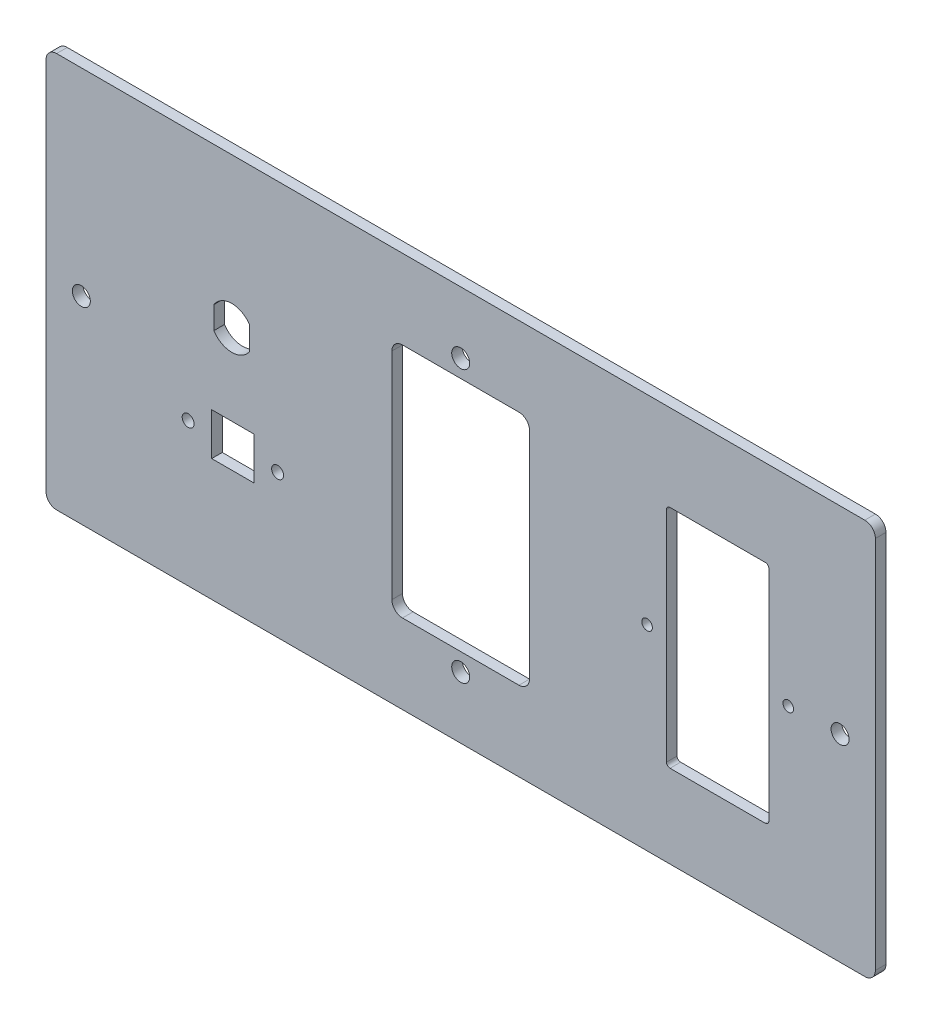
SolidWorks part; units mm, degrees
ref_plane "Front Plane" through (0, 0, 0) normal (0, 0, 1) x (1, 0, 0)
ref_plane "Top Plane" through (0, 0, 0) normal (0, 1, 0) x (1, 0, 0)
ref_plane "Right Plane" through (0, 0, 0) normal (1, 0, 0) x (0, 0, -1)
sketch "Sketch1" plane through (0, 0, 0) normal (0, 0, 1) x (1, 0, 0)
  line L0 (405.8623, -19.6394) -> (405.8623, -13.2354)
  line L1 (482.1408, 3.5626) -> (449.1408, 3.5626)
  line L2 (485.1408, 0.5626) -> (485.1408, -60.4374)
  line L3 (482.1408, -63.4374) -> (449.1408, -63.4374)
  line L4 (401.0848, -35.0851) -> (401.0848, -64.7571) construction
  line L5 (395.0848, -39.3556) -> (407.0848, -39.3556)
  line L6 (395.0848, -39.3556) -> (395.0848, -51.3556)
  line L7 (446.1408, 0.5626) -> (446.1408, -60.4374)
  line L8 (485.1408, 3.5626) -> (446.1408, -63.4374) construction
  line L9 (485.1408, -63.4374) -> (446.1408, 3.5626) construction
  line L11 (395.714, -13.2354) -> (395.714, -19.6394)
  line L19 (395.0848, -51.3556) -> (407.0848, -51.3556)
  line L21 (407.0848, -39.3556) -> (407.0848, -51.3556)
  line L22 (421.0756, -45.3556) -> (378.9661, -45.3556) construction
  line L24 (551.9531, 1.5878) -> (524.9531, 1.5878)
  line L25 (552.9531, 0.5878) -> (552.9531, -61.4122)
  line L26 (551.9531, -62.4122) -> (524.9531, -62.4122)
  line L27 (523.9531, 0.5878) -> (523.9531, -61.4122)
  line L28 (552.9531, 1.5878) -> (523.9531, -62.4122) construction
  line L29 (552.9531, -62.4122) -> (523.9531, 1.5878) construction
  line L30 (580.1408, 26.0626) -> (351.1408, 26.0626)
  line L31 (583.1408, 23.0626) -> (583.1408, -82.9374)
  line L32 (580.1408, -85.9374) -> (351.1408, -85.9374)
  line L33 (348.1408, 23.0626) -> (348.1408, -82.9374)
  line L34 (583.1408, 26.0626) -> (348.1408, -85.9374) construction
  line L35 (583.1408, -85.9374) -> (348.1408, 26.0626) construction
  arc A0 (446.1408, 0.5626) -> (449.1408, 3.5626) centre (449.1408, 0.5626) cw
  arc A1 (449.1408, -63.4374) -> (446.1408, -60.4374) centre (449.1408, -60.4374) cw
  arc A2 (482.1408, -63.4374) -> (485.1408, -60.4374) centre (482.1408, -60.4374) ccw
  arc A3 (485.1408, 0.5626) -> (482.1408, 3.5626) centre (482.1408, 0.5626) ccw
  circle A4 centre (465.6408, 8.5626) radius 2.55
  circle A5 centre (465.6408, -68.4374) radius 2.55
  arc A6 (405.8623, -13.2354) -> (395.714, -13.2354) centre (400.7881, -16.4374) ccw
  arc A7 (395.714, -19.6394) -> (405.8623, -19.6394) centre (400.7881, -16.4374) ccw
  circle A16 centre (388.4102, -45.3556) radius 1.69
  circle A17 centre (413.7594, -45.3556) radius 1.69
  arc A18 (552.9531, -61.4122) -> (551.9531, -62.4122) centre (551.9531, -61.4122) cw
  arc A19 (524.9531, -62.4122) -> (523.9531, -61.4122) centre (524.9531, -61.4122) cw
  arc A20 (523.9531, 0.5878) -> (524.9531, 1.5878) centre (524.9531, 0.5878) cw
  arc A21 (552.9531, 0.5878) -> (551.9531, 1.5878) centre (551.9531, 0.5878) ccw
  circle A22 centre (518.4531, -30.4122) radius 1.5
  circle A23 centre (558.4531, -30.4122) radius 1.5
  arc A25 (351.1408, 26.0626) -> (348.1408, 23.0626) centre (351.1408, 23.0626) ccw
  arc A26 (348.1408, -82.9374) -> (351.1408, -85.9374) centre (351.1408, -82.9374) ccw
  arc A27 (580.1408, -85.9374) -> (583.1408, -82.9374) centre (580.1408, -82.9374) ccw
  arc A28 (583.1408, 23.0626) -> (580.1408, 26.0626) centre (580.1408, 23.0626) ccw
  circle A29 centre (573.1408, -29.9374) radius 2.55
  circle A30 centre (358.1408, -29.9374) radius 2.55
  point P0 (0, 0)
  point P2 (465.6408, -29.9374)
  point P64 (538.4531, -30.4122)
  dimension "D6" = 3
  dimension "D7" = 77
  dimension "D8" = 38.5
  dimension "D9" = 5.1
  dimension "D10" = 5.1
  dimension "D22" = 3.38
  dimension "D23" = 3.38
  dimension "D24" = 12
  dimension "D26" = 12.6746
  dimension "D21" = 25.3492
  dimension "D32" = 1
  dimension "D33" = 40
  dimension "D34" = 20
  dimension "D35" = 112
  dimension "D36" = 235
  dimension "D37" = 3
  dimension "D38" = 10
  dimension "D39" = 10
  dimension "D41" = 56
  dimension "D1" = 39
  dimension "D30" = 29
  dimension "D31" = 64
  dimension "D40" = 56
  dimension "D5" = 67
extrude "Boss-Extrude1" add sketch "Sketch1" along normal blind 3
